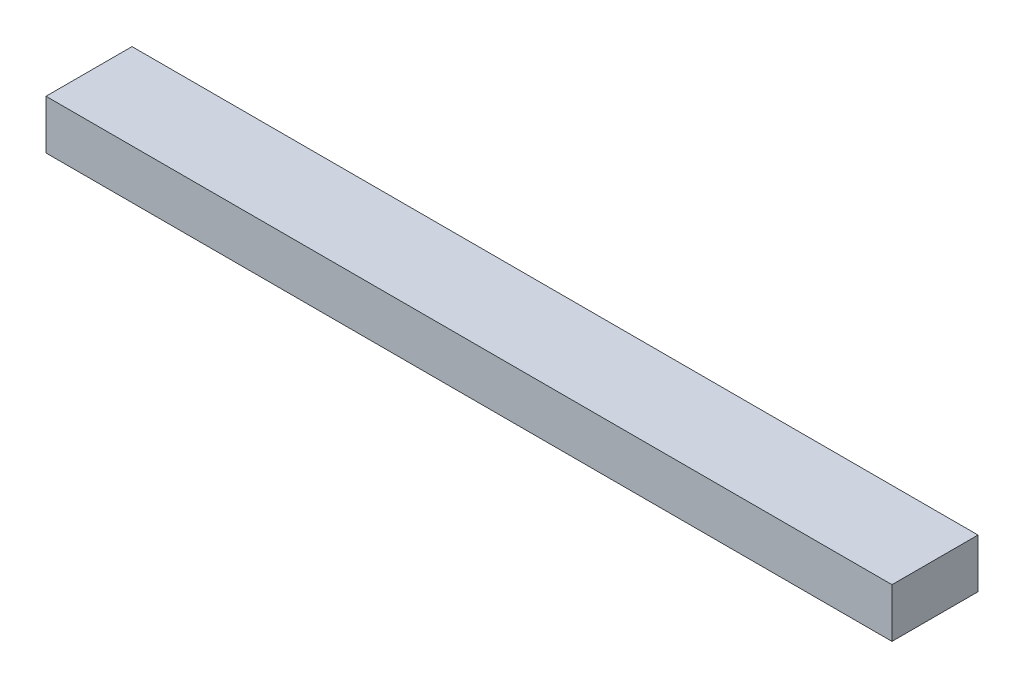
SolidWorks part; units mm, degrees
ref_plane "Front Plane" through (0, 0, 0) normal (0, 0, 1) x (1, 0, 0)
ref_plane "Top Plane" through (0, 0, 0) normal (0, 1, 0) x (1, 0, 0)
ref_plane "Right Plane" through (0, 0, 0) normal (1, 0, 0) x (0, 0, -1)
sketch "Sketch1" plane through (0, 0, 0) normal (0, 1, 0) x (1, 0, 0)
  line L1 (-437.1975, -44.45) -> (437.1975, -44.45)
  line L2 (-437.1975, -44.45) -> (-437.1975, 44.45)
  line L3 (-437.1975, 44.45) -> (437.1975, 44.45)
  line L4 (437.1975, -44.45) -> (437.1975, 44.45)
  line L5 (-437.1975, -44.45) -> (437.1975, 44.45) construction
  line L6 (-437.1975, 44.45) -> (437.1975, -44.45) construction
  point P0 (0, 0)
  dimension "D1" = 88.9
  dimension "D2" = 874.395
extrude "Boss-Extrude1" add sketch "Sketch1" along normal mid plane 50.8
